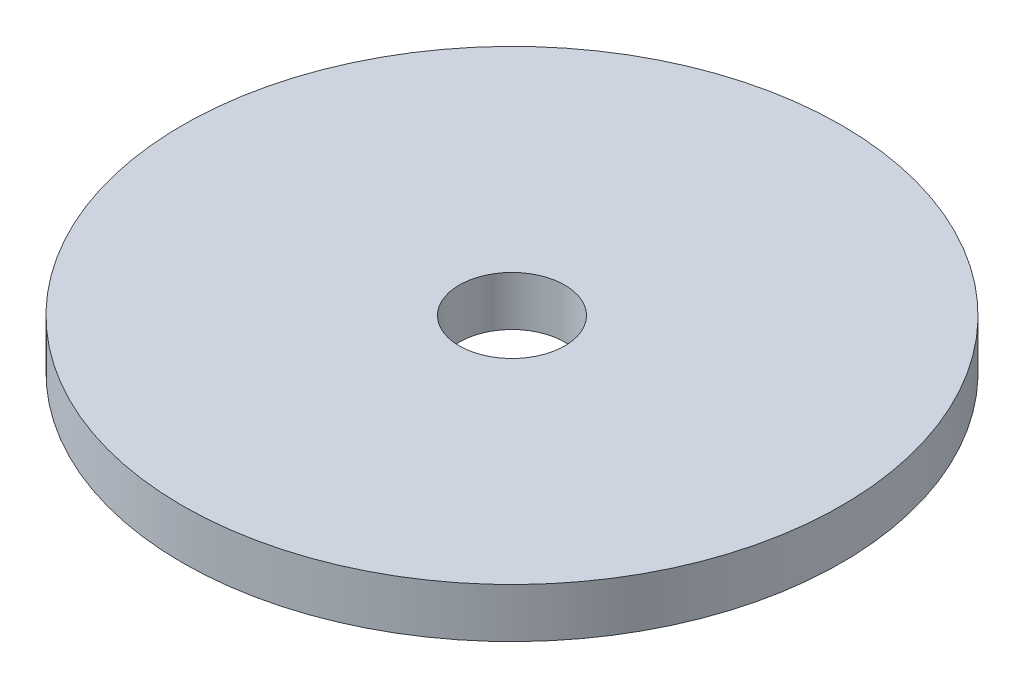
SolidWorks part; units mm, degrees
ref_plane "Alzado" through (0, 0, 0) normal (0, 0, 1) x (1, 0, 0)
ref_plane "Planta" through (0, 0, 0) normal (0, 1, 0) x (1, 0, 0)
ref_plane "Vista lateral" through (0, 0, 0) normal (1, 0, 0) x (0, 0, -1)
sketch "Croquis1" plane through (0, 0, 0) normal (0, 1, 0) x (1, 0, 0)
  circle A0 centre (0, 0) radius 3.2
  circle A1 centre (0, 0) radius 20
  dimension "D1" = 6.4
  dimension "D2" = 40
extrude "Saliente-Extruir1" add sketch "Croquis1" along normal blind 3
